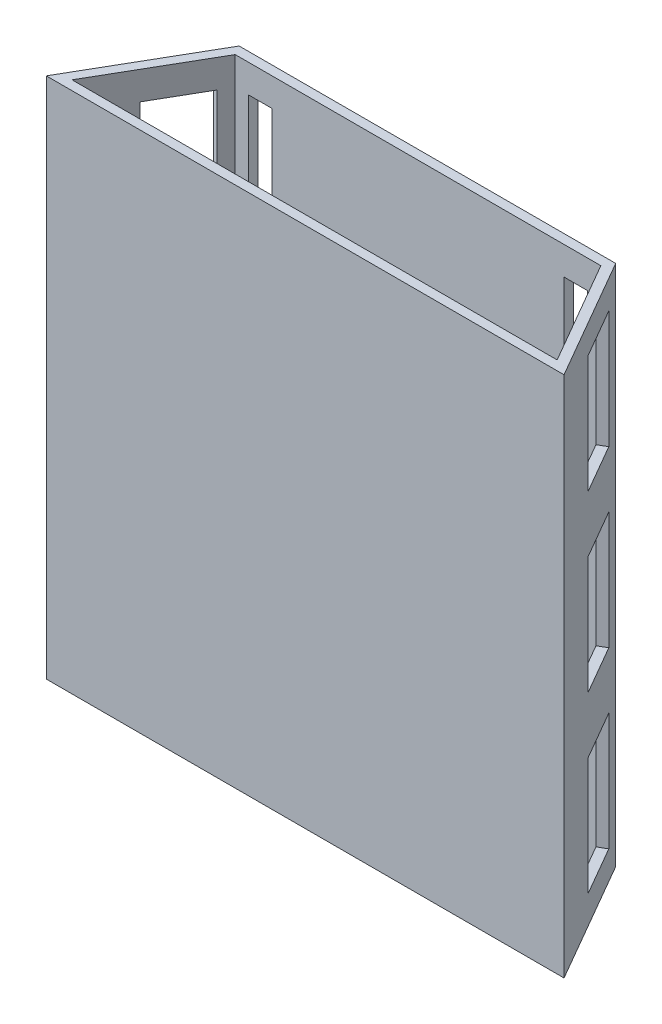
SolidWorks part; units mm, degrees
ref_plane "前基準面" through (0, 0, 0) normal (0, 0, 1) x (1, 0, 0)
ref_plane "上基準面" through (0, 0, 0) normal (0, 1, 0) x (1, 0, 0)
ref_plane "右基準面" through (0, 0, 0) normal (1, 0, 0) x (0, 0, -1)
sketch "草圖1" plane through (0, 0, 0) normal (0, 1, 0) x (1, 0, 0)
  line L0 (-13.8453, 3.6656) -> (63.8453, 3.6656)
  line L1 (-15, 5.6656) -> (65, 5.6656)
  line L3 (-15, -20.3152) -> (65, -20.3152)
  line L5 (76.5359, -18.3152) -> (63.8453, 3.6656)
  line L6 (-15, -20.3152) -> (-30, -20.3152)
  line L7 (-30, -20.3152) -> (-15, 5.6656)
  line L8 (65, -20.3152) -> (80, -20.3152)
  line L9 (80, -20.3152) -> (65, 5.6656)
  line L16 (65, -18.3152) -> (76.5359, -18.3152)
  line L17 (-15, -18.3152) -> (65, -18.3152)
  line L18 (-15, -18.3152) -> (-26.5359, -18.3152)
  line L19 (-26.5359, -18.3152) -> (-13.8453, 3.6656)
  dimension "D1" = 80
  dimension "D2" = 2
  dimension "D3" = 15
  dimension "D4" = 15
  dimension "D5" = 30
  dimension "D6" = 30
extrude "填料-伸長1" add sketch "草圖1" along normal blind 111
sketch "草圖3" plane through (51.2033, 0, -29.5622) normal (0.866, 0, -0.5) x (-0.5, 0, -0.866)
  line L0 (-57.5935, 111) -> (-27.5935, 111) construction
  line L1 (-43.5935, 105) -> (-31.5935, 105)
  line L2 (-43.5935, 105) -> (-43.5935, 80)
  line L3 (-43.5935, 80) -> (-31.5935, 80)
  line L4 (-31.5935, 105) -> (-31.5935, 80)
  line L5 (-27.5935, 111) -> (-27.5935, 0) construction
  line L6 (-43.5935, 68) -> (-31.5935, 68)
  line L7 (-43.5935, 68) -> (-43.5935, 43)
  line L8 (-43.5935, 43) -> (-31.5935, 43)
  line L9 (-31.5935, 68) -> (-31.5935, 43)
  line L10 (-43.5935, 31) -> (-31.5935, 31)
  line L11 (-43.5935, 31) -> (-43.5935, 6)
  line L12 (-43.5935, 6) -> (-31.5935, 6)
  line L13 (-31.5935, 31) -> (-31.5935, 6)
  dimension "D1" = 6
  dimension "D2" = 25
  dimension "D3" = 12
  dimension "D4" = 4
  dimension "D5" = 12
  dimension "D6" = 4
  dimension "D7" = 12
  dimension "D8" = 25
  dimension "D9" = 12
  dimension "D10" = 25
  dimension "D11" = 4
  dimension "D12" = 12
extrude "除料-伸長1" cut sketch "草圖3" against normal blind 2
sketch "草圖5" plane through (-13.7033, 0, -7.9116) normal (-0.866, 0, -0.5) x (-0.5, 0, 0.866)
  line L0 (6.5935, 105) -> (18.5935, 105)
  line L1 (6.5935, 105) -> (6.5935, 80)
  line L2 (6.5935, 80) -> (18.5935, 80)
  line L3 (18.5935, 105) -> (18.5935, 80)
  line L4 (6.5935, 68) -> (18.5935, 68)
  line L5 (6.5935, 68) -> (6.5935, 43)
  line L6 (6.5935, 43) -> (18.5935, 43)
  line L7 (18.5935, 68) -> (18.5935, 43)
  line L8 (6.5935, 31) -> (18.5935, 31)
  line L9 (6.5935, 31) -> (6.5935, 6)
  line L10 (6.5935, 6) -> (18.5935, 6)
  line L11 (18.5935, 31) -> (18.5935, 6)
  line L12 (2.5935, 111) -> (32.5935, 111) construction
  line L13 (2.5935, 111) -> (2.5935, 0) construction
  dimension "D1" = 12
  dimension "D2" = 12
  dimension "D3" = 6
  dimension "D4" = 4
  dimension "D5" = 4
  dimension "D6" = 4
  dimension "D7" = 12
  dimension "D8" = 12
  dimension "D9" = 25
  dimension "D10" = 25
  dimension "D11" = 25
  dimension "D12" = 12
extrude "除料-伸長2" cut sketch "草圖5" against normal blind 2
sketch "草圖6" plane through (0, 0, -5.6656) normal (0, 0, -1) x (-1, 0, 0)
  line L0 (-65, 111) -> (-65, 0) construction
  line L1 (-61, 105) -> (-56, 105)
  line L2 (-61, 105) -> (-61, 6)
  line L3 (-61, 6) -> (-56, 6)
  line L4 (-56, 105) -> (-56, 6)
  line L5 (6, 105) -> (11, 105)
  line L6 (6, 105) -> (6, 6)
  line L7 (6, 6) -> (11, 6)
  line L8 (11, 105) -> (11, 6)
  line L9 (15, 111) -> (15, 0) construction
  line L10 (-65, 111) -> (15, 111) construction
  line L11 (14.2894, 0) -> (-14.2894, 0) construction
  dimension "D1" = 4
  dimension "D2" = 5
  dimension "D3" = 5
  dimension "D4" = 4
  dimension "D5" = 6
  dimension "D6" = 6
  dimension "D7" = 6
  dimension "D8" = 6
extrude "除料-伸長3" cut sketch "草圖6" against normal blind 2
equation "\"ˇ0\"=60.4023"
